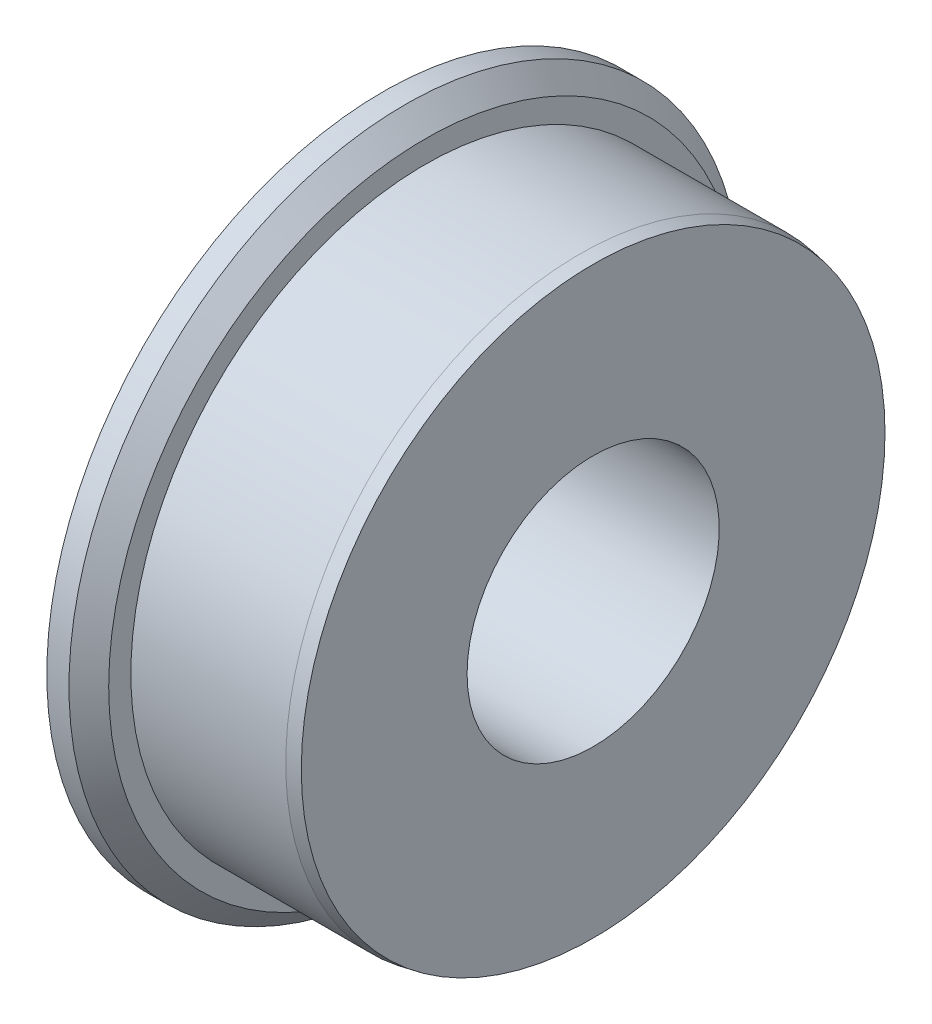
SolidWorks part; units mm, degrees
material "6061-T6 (SS)"
ref_plane "Front Plane" through (0, 0, 0) normal (0, 0, 1) x (1, 0, 0)
ref_plane "Top Plane" through (0, 0, 0) normal (0, 1, 0) x (1, 0, 0)
ref_plane "Right Plane" through (0, 0, 0) normal (1, 0, 0) x (0, 0, -1)
sketch "Sketch1" plane through (0, 0, 0) normal (1, 0, 0) x (0, 0, -1)
  circle A0 centre (0, 0) radius 25.4
  dimension "D1" = 50.8
extrude "Boss-Extrude1" add sketch "Sketch1" along normal blind 3.175
sketch "Sketch2" plane through (3.175, 0, 0) normal (1, 0, 0) x (0, 0, -1)
  circle A0 centre (0, 0) radius 22.225
  circle A1 centre (0, 0) radius 25.4 construction
  dimension "D1" = 3.175
extrude "Boss-Extrude2" add sketch "Sketch2" along normal blind 12.7
sketch "Sketch3" plane through (0, 0, 0) normal (-1, 0, 0) x (0, 0, 1)
  circle A0 centre (0, 0) radius 9.525
  dimension "D1" = 19.05
extrude "Cut-Extrude1" cut sketch "Sketch3" against normal through all
chamfer "Chamfer1" distance 1 angle 10 1 edges at (15.875, 0, -22.225)
chamfer "Chamfer2" distance 1.5 angle 45 1 edges at (3.175, 0, -25.4)
